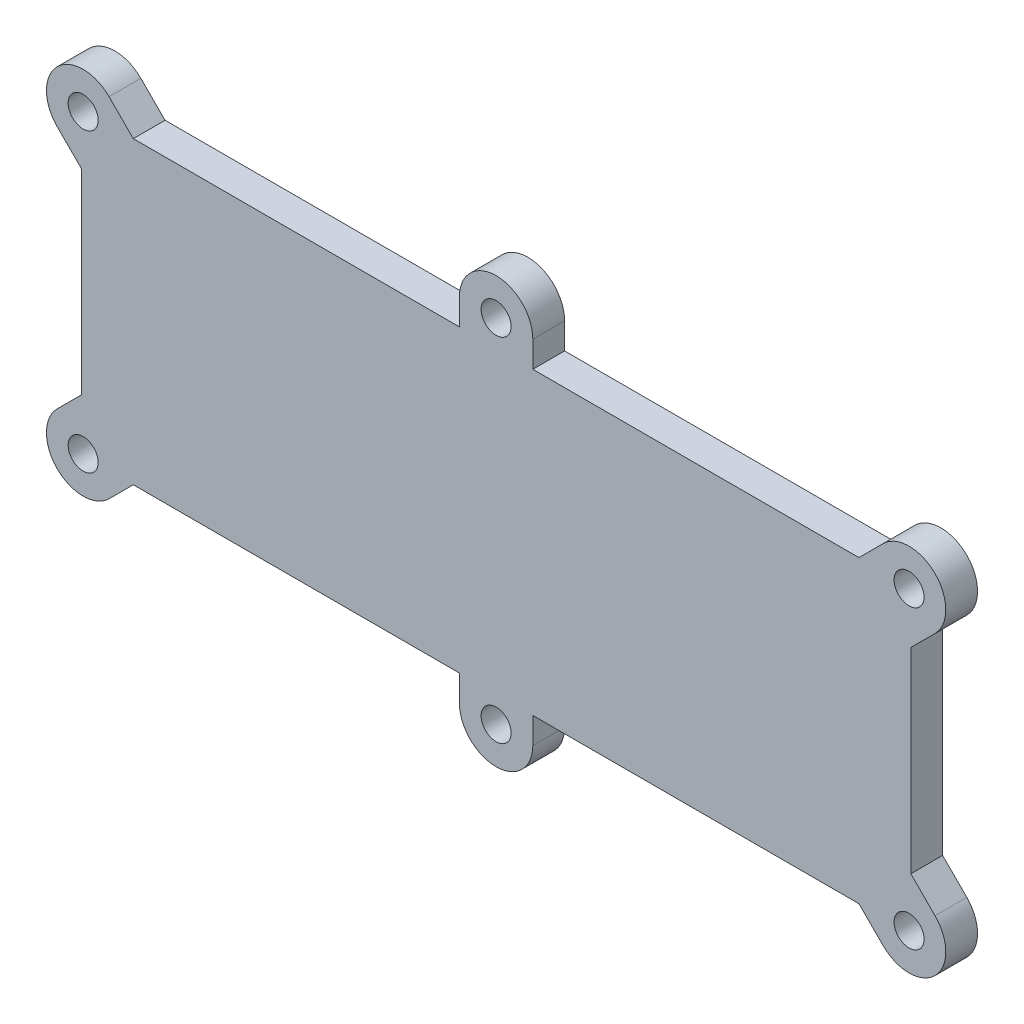
SolidWorks part; units mm, degrees
material "Acrylic (Medium-high impact)"
ref_plane "X-Y Datum" through (0, 0, 0) normal (0, 0, 1) x (1, 0, 0)
ref_plane "X-Z Datum" through (0, 0, 0) normal (0, 1, 0) x (1, 0, 0)
ref_plane "Y-Z Datum" through (0, 0, 0) normal (1, 0, 0) x (0, 0, -1)
sketch "Sketch1" plane through (0, 0, 0) normal (0, 0, 1) x (1, 0, 0)
  line L18 (166.1106, -43.3519) -> (117.2388, -43.3519)
  line L19 (117.2388, -43.3519) -> (117.2388, -39.4422)
  line L20 (106.2388, -39.4422) -> (106.2388, -43.3519)
  line L21 (106.2388, -43.3519) -> (57.367, -43.3519)
  line L22 (57.367, -43.3519) -> (53.7401, -39.725)
  line L23 (45.9619, -47.5032) -> (49.5888, -51.1301)
  line L24 (49.5888, -51.1301) -> (49.5888, -80.4988)
  line L25 (49.5888, -80.4988) -> (45.9619, -84.1257)
  line L26 (53.7401, -91.9038) -> (57.367, -88.2769)
  line L27 (57.367, -88.2769) -> (106.2388, -88.2769)
  line L28 (106.2388, -88.2769) -> (106.2388, -92.1866)
  line L29 (117.2388, -92.1866) -> (117.2388, -88.2769)
  line L30 (117.2388, -88.2769) -> (166.1106, -88.2769)
  line L31 (166.1106, -88.2769) -> (169.7375, -91.9038)
  line L32 (177.5157, -84.1257) -> (173.8888, -80.4988)
  line L33 (173.8888, -80.4988) -> (173.8888, -51.1301)
  line L34 (173.8888, -51.1301) -> (177.5157, -47.5032)
  line L35 (169.7375, -39.725) -> (166.1106, -43.3519)
  line L36 (166.1106, -43.3519) -> (117.2388, -43.3519)
  line L37 (117.2388, -43.3519) -> (117.2388, -39.4422)
  line L38 (106.2388, -39.4422) -> (106.2388, -43.3519)
  line L39 (106.2388, -43.3519) -> (57.367, -43.3519)
  line L40 (57.367, -43.3519) -> (53.7401, -39.725)
  line L41 (45.9619, -47.5032) -> (49.5888, -51.1301)
  line L42 (49.5888, -51.1301) -> (49.5888, -80.4988)
  line L43 (49.5888, -80.4988) -> (45.9619, -84.1257)
  line L44 (53.7401, -91.9038) -> (57.367, -88.2769)
  line L45 (57.367, -88.2769) -> (106.2388, -88.2769)
  line L46 (106.2388, -88.2769) -> (106.2388, -92.1866)
  line L47 (117.2388, -92.1866) -> (117.2388, -88.2769)
  line L48 (117.2388, -88.2769) -> (166.1106, -88.2769)
  line L49 (166.1106, -88.2769) -> (169.7375, -91.9038)
  line L50 (177.5157, -84.1257) -> (173.8888, -80.4988)
  line L51 (173.8888, -80.4988) -> (173.8888, -51.1301)
  line L52 (173.8888, -51.1301) -> (177.5157, -47.5032)
  line L53 (169.7375, -39.725) -> (166.1106, -43.3519)
  arc A6 (117.2388, -39.4422) -> (106.2388, -39.4422) centre (111.7388, -39.4422) ccw
  arc A7 (53.7401, -39.725) -> (45.9619, -47.5032) centre (49.851, -43.6141) ccw
  arc A8 (45.9619, -84.1257) -> (53.7401, -91.9038) centre (49.851, -88.0147) ccw
  arc A9 (106.2388, -92.1866) -> (117.2388, -92.1866) centre (111.7388, -92.1866) ccw
  arc A10 (169.7375, -91.9038) -> (177.5157, -84.1257) centre (173.6266, -88.0147) ccw
  arc A11 (177.5157, -47.5032) -> (169.7375, -39.725) centre (173.6266, -43.6141) ccw
  arc A12 (117.2388, -39.4422) -> (106.2388, -39.4422) centre (111.7388, -39.4422) ccw
  arc A13 (53.7401, -39.725) -> (45.9619, -47.5032) centre (49.851, -43.6141) ccw
  arc A14 (45.9619, -84.1257) -> (53.7401, -91.9038) centre (49.851, -88.0147) ccw
  arc A15 (106.2388, -92.1866) -> (117.2388, -92.1866) centre (111.7388, -92.1866) ccw
  arc A16 (169.7375, -91.9038) -> (177.5157, -84.1257) centre (173.6266, -88.0147) ccw
  arc A17 (177.5157, -47.5032) -> (169.7375, -39.725) centre (173.6266, -43.6141) ccw
  dimension "D1" = 0
extrude "Boss-Extrude1" add sketch "Sketch1" along normal blind 4.7625
hole_wizard "M4 Clearance Hole1" positions "Sketch3" profile "Sketch4" hole size "M4" standard "ANSI Metric" end condition through all
sketch "Sketch3" plane through (0, 0, 4.7625) normal (0, 0, 1) x (1, 0, 0)
  point P0 (111.7388, -39.4422)
  point P3 (173.6266, -43.6141)
  point P6 (173.6266, -88.0147)
  point P9 (111.7388, -92.1866)
  point P12 (49.851, -88.0147)
  point P15 (49.851, -43.6141)
sketch "Sketch4" plane through (111.7388, -39.4422, 4.7625) normal (1, 0, 0) x (0, -1, 0)
  line L0 (0, 0) -> (0, 4.7625)
  line L1 (0, 4.7625) -> (2.25, 4.7625)
  line L2 (2.25, 4.7625) -> (2.25, 0)
  line L5 (2.25, 0) -> (0, 0)
  line L11 (0, -6.35) -> (0, 107.95) construction
  dimension "Thru Hole Dia." = 4.5
  dimension "Thru Hole Depth" = 4.7625
